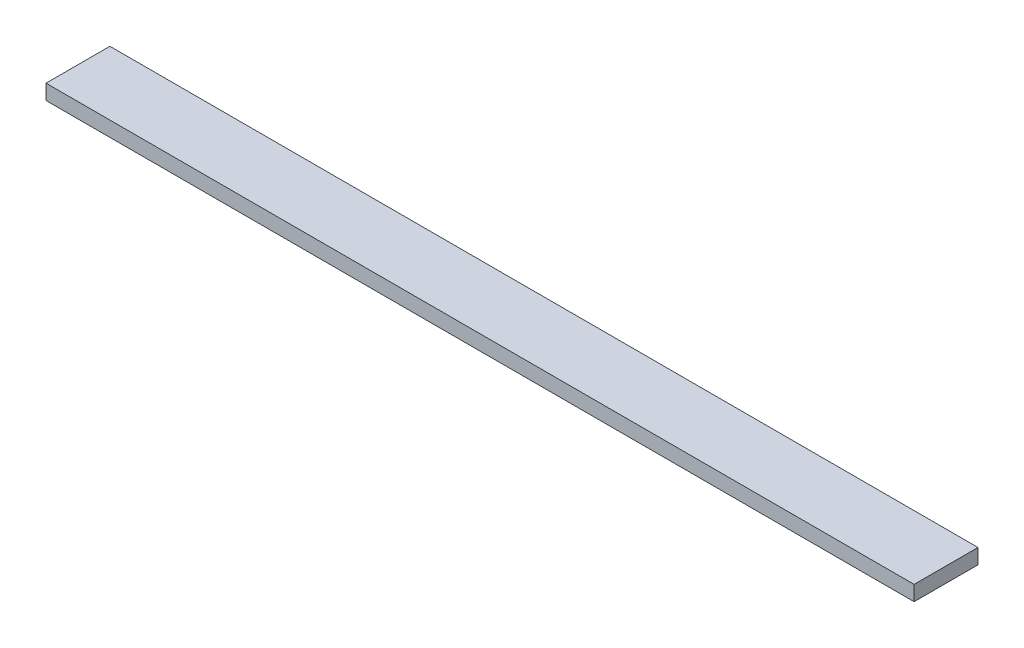
SolidWorks part; units mm, degrees
ref_plane "前基準面" through (0, 0, 0) normal (0, 0, 1) x (1, 0, 0)
ref_plane "上基準面" through (0, 0, 0) normal (0, 1, 0) x (1, 0, 0)
ref_plane "右基準面" through (0, 0, 0) normal (1, 0, 0) x (0, 0, -1)
sketch "草圖1" plane through (0, 0, 0) normal (0, 1, 0) x (1, 0, 0)
  line L1 (-5775, 425) -> (5775, 425)
  line L2 (-5775, 425) -> (-5775, -425)
  line L3 (-5775, -425) -> (5775, -425)
  line L4 (5775, 425) -> (5775, -425)
  line L5 (-5775, 425) -> (5775, -425) construction
  line L6 (-5775, -425) -> (5775, 425) construction
  point P0 (0, 0)
  dimension "D1" = 11550
  dimension "D2" = 850
extrude "填料-伸長1" add sketch "草圖1" along normal blind 200
